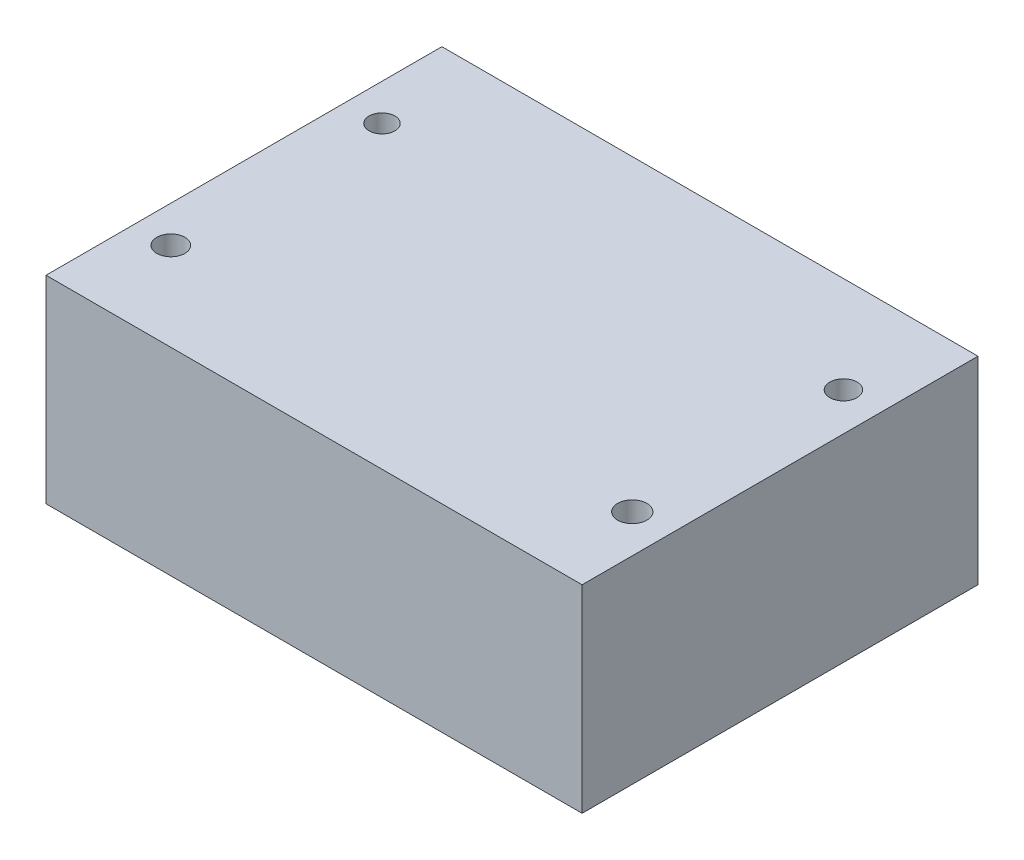
SolidWorks part; units mm, degrees
ref_plane "Płaszczyzna przednia" through (0, 0, 0) normal (0, 0, 1) x (1, 0, 0)
ref_plane "Płaszczyzna górna" through (0, 0, 0) normal (0, 1, 0) x (1, 0, 0)
ref_plane "Płaszczyzna prawa" through (0, 0, 0) normal (1, 0, 0) x (0, 0, -1)
sketch "Sketch1" plane through (0, 0, 0) normal (0, 1, 0) x (1, 0, 0)
  line L1 (-32.5, -13.1786) -> (32.5, -13.1786)
  line L2 (-32.5, -13.1786) -> (-32.5, 34.8214)
  line L3 (-32.5, 34.8214) -> (32.5, 34.8214)
  line L4 (32.5, -13.1786) -> (32.5, 34.8214)
  dimension "D1" = 65
  dimension "D2" = 48
extrude "Boss-Extrude2" add sketch "Sketch1" along normal blind 24
sketch "Sketch2" plane through (0, 24, 0) normal (0, 1, 0) x (1, 0, 0)
  circle A0 centre (-28.0721, 23.1294) radius 1.566
  circle A1 centre (27.8753, 23.1294) radius 1.6482
  circle A2 centre (27.8753, -2.4727) radius 1.7722
  circle A3 centre (-28.0721, -2.4727) radius 1.7021
extrude "Cut-Extrude1" cut sketch "Sketch2" against normal blind 30
